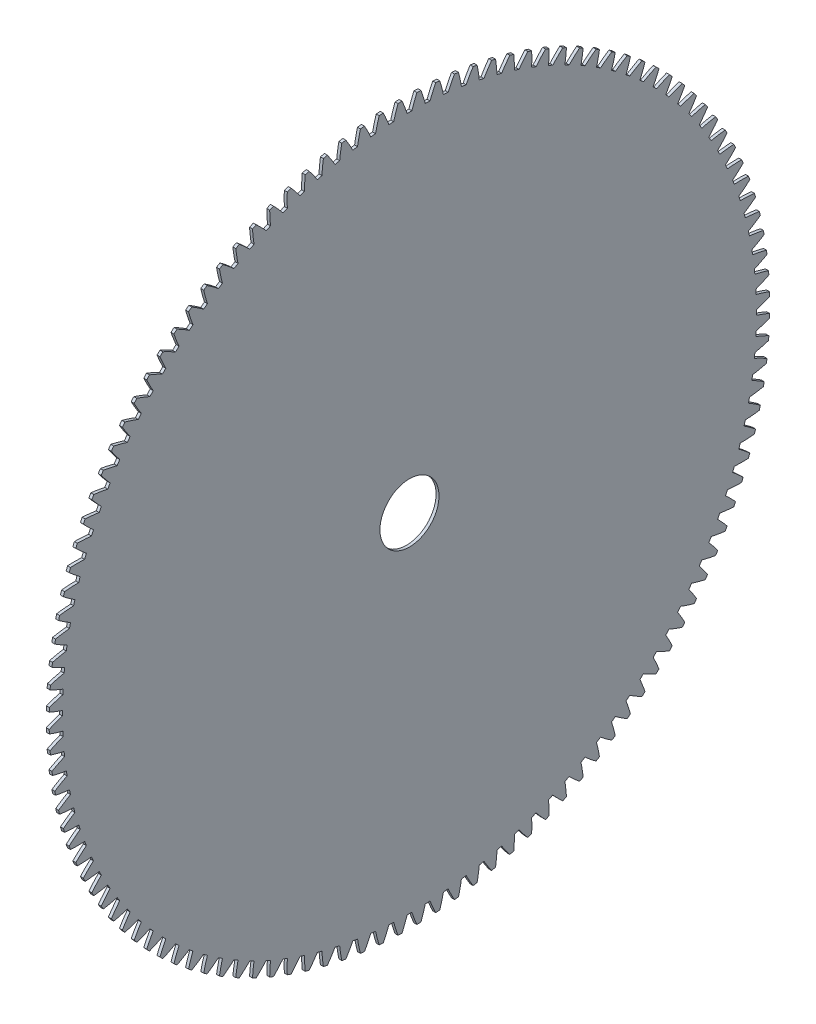
SolidWorks part; units mm, degrees
ref_plane "Plane1" through (0, 0, 0) normal (0, 0, 1) x (1, 0, 0)
ref_plane "Plane2" through (0, 0, 0) normal (0, 1, 0) x (1, 0, 0)
ref_plane "Plane3" through (0, 0, 0) normal (1, 0, 0) x (0, 0, -1)
other "Configuration Table"
sketch "HoldingSke" plane through (0, 0, 0) normal (0, 1, 0) x (1, 0, 0)
  line L0 (0, 0) -> (-0.0833, -0.1443)
  line L1 (-15, 0) -> (100, 0) construction
  line L2 (0, 0) -> (-2.1039, 2.3779)
  line L3 (0, 0) -> (-11.863, 4.5341)
  line L4 (0, 0) -> (-4.318, 7.479)
  line L5 (0, 0) -> (-46.8476, -17.4728)
  line L6 (0, 0) -> (-2.4869, -1.6779)
  line L7 (-2.1039, 2.3779) -> (8.6586, 51.2059)
  line L8 (-76.2, 54.61) -> (-71.8, 54.61)
  line L9 (-71.009, 38.7566) -> (-53.1078, 45.2721)
  line L10 (-76.2, 71.12) -> (104.1128, 71.12)
  line L11 (0, 0) -> (-3, 0)
  line L12 (-76.2, 101.6) -> (-75.993, 101.6)
  line L13 (24.9733, 27.94) -> (52.9518, 28.4284)
  line L14 (24.9733, 27.94) -> (24.9743, 27.94)
  line L15 (24.9733, 27.94) -> (100.4006, 29.5858)
  line L16 (-63.627, -6) -> (-12.827, -6)
  circle A0 centre (0, 0) radius 30
  circle A1 centre (0, 0) radius 37.5
  circle A2 centre (0, 0) radius 37.5
  circle A3 centre (0, 0) radius 30
  dimension "MHD" = 75
  dimension "Hub_dia" = 75
  dimension "Bore" = 60
  dimension "MBD" = 60
  dimension "Num_teeth" = 120
  dimension "Pitch" = 0.1667
  dimension "Overall_len" = 50
  dimension "Show_teeth" = 120
  dimension "Thickness" = 3
  dimension "OAL" = 50.0001
  dimension "T_dim" = 4.4
  dimension "Ap" = 20
  dimension "H" = 19.05
  dimension "Pitch_radius" = 180.3128
  dimension "Width" = 3
  dimension "Backlash" = 0.207
  dimension "Addendum_fac" = 1
  dimension "Dedendum_fac" = 1.25
  dimension "Clearance_fac" = 0.25
  dimension "Dedendum_add" = 0.001
  dimension "Module" = 6
sketch "BasProSke" plane through (0, 0, 0) normal (0, 1, 0) x (1, 0, 0)
  line L0 (-10, 0) -> (60, 0) construction
  line L1 (0, 0) -> (0, 366)
  line L2 (0, 0) -> (3, 0)
  line L3 (3, 0) -> (3, 366)
  line L4 (3, 366) -> (0, 366)
  dimension "Thickness" = 3
  dimension "Diameter" = 732
revolve "Base-Revolve" add sketch "BasProSke" angle 360 about L0
sketch "TooCutSke" plane through (0, 0, 0) normal (1, 0, 0) x (0, 0, -1)
  line L1 (0, 0) -> (0, 107) construction
  line L2 (0, 0) -> (-5.0745, 359.9642) construction
  line L3 (0, 0) -> (-18.846, 719.7007) construction
  line L4 (-5.0745, 359.9642) -> (-9.423, 359.8504) construction
  arc A0 (2.4299, 352.4906) -> (-2.4299, 352.4906) centre (0, 0) ccw
  arc A1 (7.5348, 365.9478) -> (-7.5348, 365.9478) centre (0, 0) ccw
  circle A2 centre (0, 0) radius 360 construction
  circle A3 centre (0, 0) radius 338.2893 construction
  arc A4 (-2.4299, 352.4906) -> (-7.5348, 365.9478) centre (-139.4523, 308.2089) ccw
  arc A5 (7.5348, 365.9478) -> (2.4299, 352.4906) centre (139.4523, 308.2089) ccw
  dimension "Root_dia" = 704.998
  dimension "Overcut_dia" = 732.0508
  dimension "Pitch_dia" = 720
  dimension "Base_dia" = 676.5787
  dimension "Flank_rad" = 144
  dimension "Half_ang" = 1.5
  dimension "Half_CT" = 4.35
extrude "ToothCut" cut sketch "TooCutSke" along normal through all
fillet "Breaks" [suppressed] radius 0.12
fillet "RootFillets" [suppressed] radius 1.501
pattern_circular "TeethCuts" count 120 every 3 about axis through (-10, 0, 0) along (1, 0, 0) of "ToothCut", "RootFillets", "Breaks"
sketch "HubNeaOneSke" plane through (0, 0, 0) normal (-1, 0, 0) x (0, 0, 1)
  circle A0 centre (0, 0) radius 37.5
  dimension "Diameter" = 75
extrude "HubNearOne" [suppressed] add sketch "HubNeaOneSke" along normal blind 47.0001
sketch "HubNeaBotSke" plane through (0, 0, 0) normal (-1, 0, 0) x (0, 0, 1)
  circle A0 centre (0, 0) radius 37.5
  dimension "Diameter" = 75
extrude "HubNearBoth" [suppressed] add sketch "HubNeaBotSke" along normal blind 23.5
ref_plane "FarPln" through (3, 0, 0) normal (1, 0, 0) x (0, 0, -1)
sketch "HubFarSke" plane through (3, 0, 0) normal (1, 0, 0) x (0, 0, -1)
  circle A0 centre (0, 0) radius 37.5
  dimension "Diameter" = 75
extrude "HubFar" [suppressed] add sketch "HubFarSke" along normal blind 23.5
sketch "BorSke" plane through (0, 0, 0) normal (1, 0, 0) x (0, 0, -1)
  circle A0 centre (0, 0) radius 30
  dimension "Diameter" = 60
extrude "Bore" cut sketch "BorSke" along normal mid plane 100.0001
sketch "KeySke" plane through (0, 0, 0) normal (1, 0, 0) x (0, 0, -1)
  line L0 (-9, 0) -> (-9, 34.4)
  line L1 (-9, 34.4) -> (9, 34.4)
  line L2 (9, 34.4) -> (9, 0)
  line L3 (0, 0) -> (0, 34) construction
  line L4 (-9, 0) -> (9, 0)
  dimension "Offset" = 34.4
  dimension "Width" = 18
extrude "Keyway" [suppressed] cut sketch "KeySke" along normal mid plane 100.0001
pattern_circular "Keyway2" [suppressed] count 2 every 90 about axis through (-10, 0, 0) along (1, 0, 0)
sketch "Sketch1" plane through (3, 0, 0) normal (1, 0, 0) x (0, 0, -1)
  line L0 (-30.7668, 364.7045) -> (-32.7711, -357.8048)
  arc A0 (-34.4287, -350.8136) -> (-30.7668, -364.7045) centre (106.4717, -321.0973) ccw construction
  dimension "D1" = 722.5093
equation "' \"Module@HoldingSke\" = 6.35"
equation "' \"Num_teeth@HoldingSke\" = 12"
equation "' \"Ap@HoldingSke\" =  20"
equation "' \"Ap@HoldingSke\" = 20"
equation "' \"Width@HoldingSke\" = 0.5 * 25.4"
equation "' \"Hub_dia@HoldingSke\"= 1 * 25.4"
equation "' \"Hub_dia@HoldingSke\" = 1 * 25.4"
equation "' \"Overall_len@HoldingSke\" = 1.0 * 25.4"
equation "' \"Bore@HoldingSke\" = 0.75 * 25.4"
equation "' \"T_dim@HoldingSke\" = 0.1 * 25.4"
equation "' \"Width@KeySke\" = 0.25 * 25.4"
equation "' \"Show_teeth@HoldingSke\" = 13"
equation "' \"Backlash@HoldingSke\" = 0.009 * 25.4"
equation "' \"Addendum_fac@HoldingSke\" = 1.0"
equation "' \"Dedendum_fac@HoldingSke\" = 1.25"
equation "' \"Dedendum_add@HoldingSke\" = 0.00005 * 25.4"
equation "' \"Clearance_fac@HoldingSke\" = 0.25"
equation "\"Pitch@HoldingSke\" = 1 / \"Module@HoldingSke\""
equation "\"Overcut_dia@TooCutSke\" = (\"Num_teeth@HoldingSke\" + 2 * \"Addendum_fac@HoldingSke\") / \"Pitch@HoldingSke\" + 0.002 * 25.4"
equation "\"Pitch_dia@TooCutSke\" = \"Num_teeth@HoldingSke\" / \"Pitch@HoldingSke\""
equation "\"Base_dia@TooCutSke\" = \"Num_teeth@HoldingSke\" / \"Pitch@HoldingSke\" * cos((\"Ap@HoldingSke\"  * 3.14159265 / 180))"
equation "\"Root_dia@TooCutSke\" = (\"Num_teeth@HoldingSke\" + 2) / \"Pitch@HoldingSke\" - 2 * (\"Addendum_fac@HoldingSke\" + \"Dedendum_fac@HoldingSke\") / \"Pitch@HoldingSke\" - \"Dedendum_add@HoldingSke\" * 2"
equation "\"Half_ang@TooCutSke\" = 180 / \"Num_teeth@HoldingSke\""
equation "\"Half_CT@TooCutSke\" = \"Num_teeth@HoldingSke\" / \"Pitch@HoldingSke\" * sin((3.14159265 / 2 / \"Num_teeth@HoldingSke\")) / 2 - 7 * \"Backlash@HoldingSke\" / 4"
equation "\"Flank_rad@TooCutSke\" = \"Num_teeth@HoldingSke\" / \"Pitch@HoldingSke\" / 5"
equation "\"Radius@RootFillets\" = \"Clearance_fac@HoldingSke\" / \"Pitch@HoldingSke\" + \"Dedendum_add@HoldingSke\""
equation "\"Break_rad@Breaks\" = 0.02 / \"Pitch@HoldingSke\""
equation "\"Thickness@HoldingSke\" = \"Width@HoldingSke\""
equation "\"OAL@HoldingSke\" = \"Thickness@HoldingSke\""
equation "\"MHD@HoldingSke\" = (\"Num_teeth@HoldingSke\" + 2) / \"Pitch@HoldingSke\" - 2 * (\"Addendum_fac@HoldingSke\" + \"Dedendum_fac@HoldingSke\")  / \"Pitch@HoldingSke\" - \"Dedendum_add@HoldingSke\" * 2"
equation "\"MBD@HoldingSke\" = (\"Num_teeth@HoldingSke\" + 2) / \"Pitch@HoldingSke\" - 2 * (\"Addendum_fac@HoldingSke\" + \"Dedendum_fac@HoldingSke\")  / \"Pitch@HoldingSke\" - \"Dedendum_add@HoldingSke\" * 2 - 0.002 * 25.4"
equation "\"MHD@HoldingSke\" = ((sgn( \"MHD@HoldingSke\" - \"Hub_dia@HoldingSke\" )-1)*( \"MHD@HoldingSke\" - \"Hub_dia@HoldingSke\" ))/-2+ \"Hub_dia@HoldingSke\""
equation "\"MBD@HoldingSke\" = ((sgn( \"MBD@HoldingSke\" - \"Bore@HoldingSke\" )-1)*( \"MBD@HoldingSke\" - \"Bore@HoldingSke\" ))/-2+ \"Bore@HoldingSke\""
equation "\"OAL@HoldingSke\" = ((sgn( \"OAL@HoldingSke\" - \"Overall_len@HoldingSke\" )+1)*( \"OAL@HoldingSke\" - \"Overall_len@HoldingSke\" ))/2 + \"Overall_len@HoldingSke\" + 0.000002 * 25.4"
equation "\"Num_teeth@TeethCuts\" = int( \"Show_teeth@HoldingSke\" ) + 1"
equation "\"Num_teeth@TeethCuts\" = ((sgn( \"Num_teeth@TeethCuts\" - \"Num_teeth@HoldingSke\" )-1)*( \"Num_teeth@TeethCuts\" - \"Num_teeth@HoldingSke\" ))/-2+ \"Num_teeth@HoldingSke\""
equation "\"Num_teeth@TeethCuts\" = ((sgn( \"Num_teeth@TeethCuts\" - 2.0)+1)*( \"Num_teeth@TeethCuts\" - 2.0))/2 +2.0"
equation "\"Angle@TeethCuts\" = 360.0 / \"Num_teeth@HoldingSke\""
equation "\"Diameter@BasProSke\" = (\"Num_teeth@HoldingSke\" + 2 * \"Addendum_fac@HoldingSke\") / \"Pitch@HoldingSke\""
equation "\"Thickness@BasProSke\"  = \"Thickness@HoldingSke\""
equation "' \"Fillet_rad@BasProSke\" =  \"Thickness@HoldingSke\" * 0.05"
equation "' \"Fillet_rad@BasProSke\" = \"Thickness@HoldingSke\" * 0.05"
equation "\"MHD@HoldingSke\" = ((sgn( \"MHD@HoldingSke\" - \"Root_dia@TooCutSke\" )-1)*( \"MHD@HoldingSke\" - \"Root_dia@TooCutSke\" ))/-2+ \"Root_dia@TooCutSke\""
equation "\"Diameter@HubNeaOneSke\" = \"MHD@HoldingSke\""
equation "\"Length@HubNearOne\" = \"OAL@HoldingSke\" - \"Thickness@BasProSke\""
equation "\"Diameter@HubNeaBotSke\" = \"MHD@HoldingSke\""
equation "\"Length@HubNearBoth\" = ( \"OAL@HoldingSke\" - \"Thickness@BasProSke\" ) / 2.0"
equation "\"Thickness@FarPln\" = \"Thickness@BasProSke\""
equation "\"Diameter@HubFarSke\" = \"MHD@HoldingSke\""
equation "\"Length@HubFar\" = ( \"OAL@HoldingSke\" - \"Thickness@BasProSke\" ) / 2.0"
equation "\"Diameter@BorSke\" = \"MBD@HoldingSke\""
equation "\"D1@Bore\" = \"OAL@HoldingSke\" * 2.0"
equation "\"D1@Keyway\" = \"OAL@HoldingSke\" * 2.0"
equation "\"Offset@KeySke\" = \"T_dim@HoldingSke\" + \"MBD@HoldingSke\" / 2.0"
